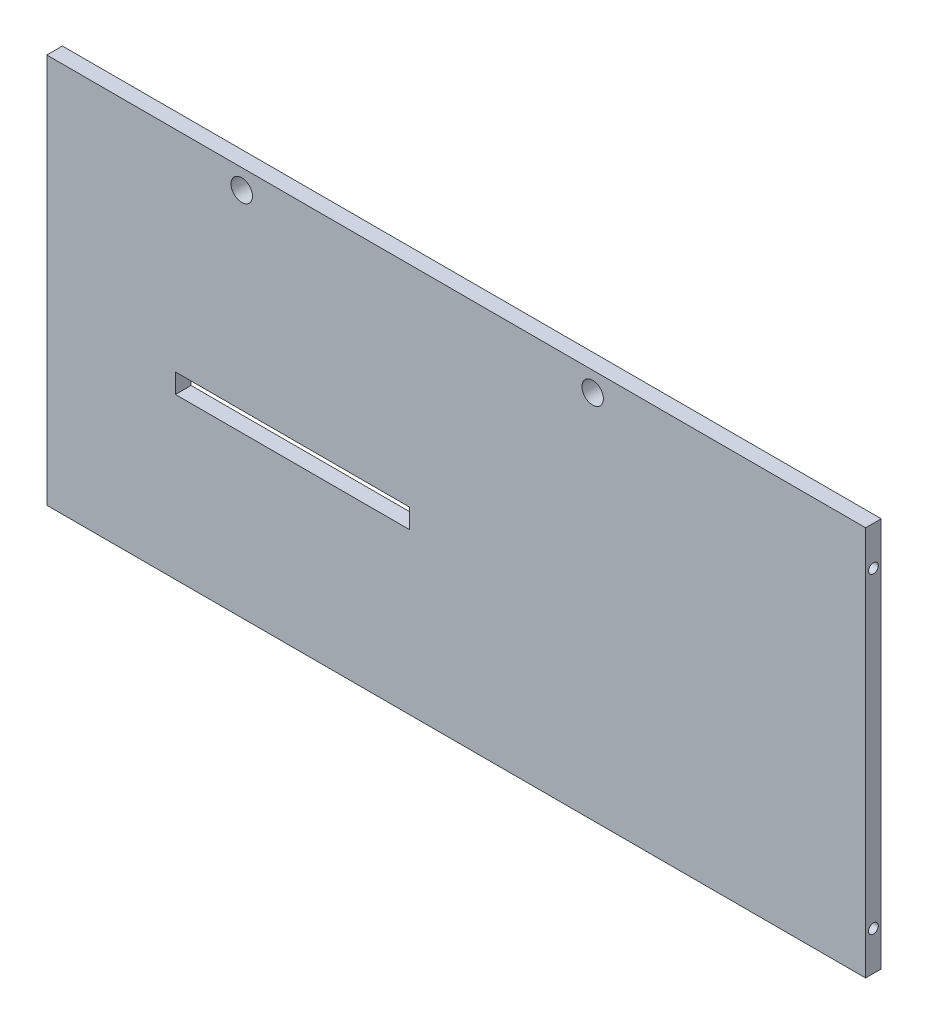
SolidWorks part; units mm, degrees
ref_plane "前视基准面" through (0, 0, 0) normal (0, 0, 1) x (1, 0, 0)
ref_plane "上视基准面" through (0, 0, 0) normal (0, 1, 0) x (1, 0, 0)
ref_plane "右视基准面" through (0, 0, 0) normal (1, 0, 0) x (0, 0, -1)
sketch "草图1" plane through (0, 0, 0) normal (0, 0, 1) x (1, 0, 0)
  line L1 (0, 0) -> (200, 0)
  line L2 (0, 0) -> (0, 100)
  line L3 (0, 100) -> (200, 100)
  line L4 (200, 0) -> (200, 100)
  dimension "D1" = 100
  dimension "D2" = 200
extrude "凸台-拉伸1" add sketch "草图1" along normal blind 4
sketch "草图5" plane through (0, 0, 0) normal (0, 0, -1) x (-1, 0, 0)
  line L0 (-200, 100) -> (0, 100) construction
  line L1 (0, 100) -> (0, 0) construction
  circle A0 centre (-50, 95) radius 2.75
  circle A1 centre (-140, 95) radius 2.75
  point P8 (0, 0)
  dimension "D1" = 5.5
  dimension "D4" = 5.5
  dimension "D2" = 5
  dimension "D3" = 50
  dimension "D5" = 90
extrude "切除-拉伸1" cut sketch "草图5" against normal through all
sketch "草图6" plane through (200, 0, 0) normal (1, 0, 0) x (0, 0, -1)
  line L1 (0, 0) -> (-4, 0)
  line L2 (0, 0) -> (0, 100)
  line L3 (0, 100) -> (-4, 100)
  line L4 (-4, 0) -> (-4, 100)
extrude "凸台-拉伸2" add sketch "草图6" along normal blind 10
sketch "草图7" plane through (0, 0, 0) normal (0, 0, -1) x (-1, 0, 0)
  line L0 (0, 100) -> (0, 0) construction
  line L1 (-33, 41.1) -> (-93, 41.1)
  line L2 (-33, 41.1) -> (-33, 46.1)
  line L3 (-33, 46.1) -> (-93, 46.1)
  line L4 (-93, 41.1) -> (-93, 46.1)
  line L5 (-210, 100) -> (0, 100) construction
  dimension "D1" = 60
  dimension "D2" = 33
  dimension "D3" = 5
  dimension "D4" = 53.9
extrude "切除-拉伸2" cut sketch "草图7" against normal blind 5
hole_wizard "M3 螺纹孔1" positions "草图8" profile "草图9" tap size "M3" standard "ISO"
sketch "草图8" plane through (0, 0, 0) normal (-1, 0, 0) x (0, 0, 1)
  point P0 (2, 10)
  point P3 (2, 90)
sketch "草图9" plane through (0, 10, 2) normal (0, 1, 0) x (0, 0, 1)
  line L0 (0, 0) -> (0, 8.2511)
  line L1 (0, 8.2511) -> (1.25, 7.5)
  line L2 (1.25, 7.5) -> (1.25, 0)
  line L5 (1.25, 0) -> (0, 0)
  line L10 (0, 8.2511) -> (-1.25, 7.5) construction
  line L11 (0, -6.35) -> (0, 107.95) construction
  dimension "螺纹孔钻头直径" = 2.5
  dimension "螺纹孔钻头深度" = 7.5
  dimension "导头角度" = 118
cosmetic thread "孔螺蚊线1" parameters "D1"=6, "D2"=3
cosmetic thread "孔螺蚊线2" parameters "D1"=6, "D2"=3
hole_wizard "M3 螺纹孔2" positions "草图10" profile "草图11" tap size "M3" standard "ISO"
sketch "草图10" plane through (210, 0, 0) normal (1, 0, 0) x (0, 0, -1)
  point P0 (-2, 10)
  point P3 (-2, 90)
sketch "草图11" plane through (210, 10, 2) normal (0, 1, 0) x (0, 0, -1)
  line L0 (0, 0) -> (0, 8.2511)
  line L1 (0, 8.2511) -> (1.25, 7.5)
  line L2 (1.25, 7.5) -> (1.25, 0)
  line L5 (1.25, 0) -> (0, 0)
  line L10 (0, 8.2511) -> (-1.25, 7.5) construction
  line L11 (0, -6.35) -> (0, 107.95) construction
  dimension "螺纹孔钻头直径" = 2.5
  dimension "螺纹孔钻头深度" = 7.5
  dimension "导头角度" = 118
cosmetic thread "孔螺蚊线3" parameters "D1"=6, "D2"=3
cosmetic thread "孔螺蚊线4" parameters "D1"=6, "D2"=3
hole_wizard "M3 螺纹孔3" positions "草图12" profile "草图13" tap size "M3" standard "ISO"
sketch "草图12" plane through (0, 0, 0) normal (0, -1, 0) x (-1, 0, 0)
  point P0 (-20, -2)
  point P3 (-190, -2)
sketch "草图13" plane through (20, 0, 2) normal (1, 0, 0) x (0, 0, -1)
  line L0 (0, 0) -> (0, 8.2511)
  line L1 (0, 8.2511) -> (1.25, 7.5)
  line L2 (1.25, 7.5) -> (1.25, 0)
  line L5 (1.25, 0) -> (0, 0)
  line L10 (0, 8.2511) -> (-1.25, 7.5) construction
  line L11 (0, -6.35) -> (0, 107.95) construction
  dimension "螺纹孔钻头直径" = 2.5
  dimension "螺纹孔钻头深度" = 7.5
  dimension "导头角度" = 118
cosmetic thread "孔螺蚊线5" parameters "D1"=6, "D2"=3
cosmetic thread "孔螺蚊线6" parameters "D1"=6, "D2"=3
